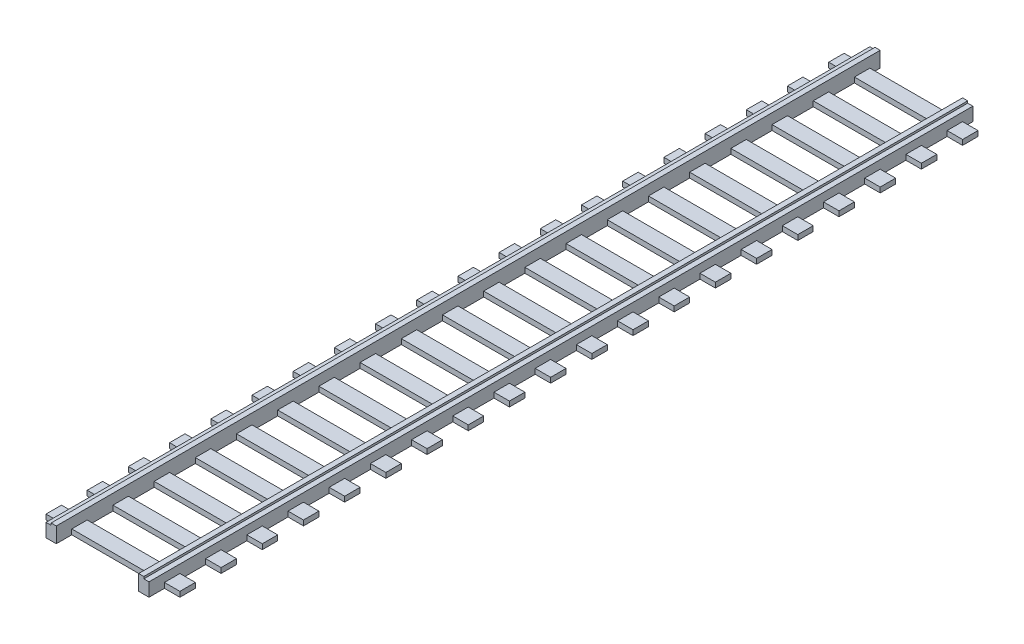
SolidWorks part; units mm, degrees
ref_plane "Front Plane" through (0, 0, 0) normal (0, 0, 1) x (1, 0, 0)
ref_plane "Top Plane" through (0, 0, 0) normal (0, 1, 0) x (1, 0, 0)
ref_plane "Right Plane" through (0, 0, 0) normal (1, 0, 0) x (0, 0, -1)
sketch "Sketch1" plane through (0, 0, 0) normal (0, 1, 0) x (1, 0, 0)
  line L1 (-43.6876, 71.25) -> (-42.6876, 71.25)
  line L2 (-43.6876, 71.25) -> (-43.6876, -88.75)
  line L3 (-43.6876, -88.75) -> (-42.6876, -88.75)
  line L4 (-42.6876, 71.25) -> (-42.6876, -88.75)
  line L5 (-26.6876, 71.25) -> (-25.6876, 71.25)
  line L6 (-26.6876, 71.25) -> (-26.6876, -88.75)
  line L7 (-26.6876, -88.75) -> (-25.6876, -88.75)
  line L8 (-25.6876, 71.25) -> (-25.6876, -88.75)
  dimension "D1" = 160
  dimension "D2" = 1
  dimension "D3" = 1
  dimension "D4" = 16
extrude "Boss-Extrude1" add sketch "Sketch1" along normal blind 3
sketch "Sketch2" plane through (0, 0, 0) normal (0, -1, 0) x (1, 0, 0)
  line L0 (-43.6876, -71.25) -> (-43.6876, 88.75) construction
  line L1 (-43.6876, -71.25) -> (-43.6876, 88.75)
  line L2 (-44.6876, -71.25) -> (-44.6876, 88.75)
  line L3 (-43.6876, -71.25) -> (-44.6876, -71.25)
  line L4 (-43.6876, 88.75) -> (-44.6876, 88.75)
  line L5 (-25.6876, 88.75) -> (-25.6876, -71.25) construction
  line L6 (-25.6876, 88.75) -> (-25.6876, -71.25)
  line L7 (-24.6876, 88.75) -> (-24.6876, -71.25)
  line L8 (-25.6876, 88.75) -> (-24.6876, 88.75)
  line L9 (-25.6876, -71.25) -> (-24.6876, -71.25)
  dimension "D1" = 1
  dimension "D2" = 1
extrude "Boss-Extrude2" add sketch "Sketch2" against normal blind 2.6
sketch "Sketch3" plane through (0, 0, 0) normal (0, -1, 0) x (1, 0, 0)
  line L0 (-44.6876, 88.75) -> (-44.6876, -71.25) construction
  line L1 (-47.6876, 85.75) -> (-21.6876, 85.75)
  line L2 (-47.6876, 85.75) -> (-47.6876, 82.75)
  line L3 (-47.6876, 82.75) -> (-21.6876, 82.75)
  line L4 (-21.6876, 85.75) -> (-21.6876, 82.75)
  line L5 (-24.6876, -71.25) -> (-24.6876, 88.75) construction
  line L6 (-47.6876, 77.75) -> (-47.6876, 74.75)
  line L7 (-47.6876, 77.75) -> (-21.6876, 77.75)
  line L8 (-21.6876, 77.75) -> (-21.6876, 74.75)
  line L9 (-47.6876, 74.75) -> (-21.6876, 74.75)
  line L10 (-47.6876, 69.75) -> (-47.6876, 66.75)
  line L11 (-47.6876, 69.75) -> (-21.6876, 69.75)
  line L12 (-21.6876, 69.75) -> (-21.6876, 66.75)
  line L13 (-47.6876, 66.75) -> (-21.6876, 66.75)
  line L14 (-47.6876, 61.75) -> (-47.6876, 58.75)
  line L15 (-47.6876, 61.75) -> (-21.6876, 61.75)
  line L16 (-21.6876, 61.75) -> (-21.6876, 58.75)
  line L17 (-47.6876, 58.75) -> (-21.6876, 58.75)
  line L18 (-47.6876, 53.75) -> (-47.6876, 50.75)
  line L19 (-47.6876, 53.75) -> (-21.6876, 53.75)
  line L20 (-21.6876, 53.75) -> (-21.6876, 50.75)
  line L21 (-47.6876, 50.75) -> (-21.6876, 50.75)
  line L22 (-47.6876, 45.75) -> (-47.6876, 42.75)
  line L23 (-47.6876, 45.75) -> (-21.6876, 45.75)
  line L24 (-21.6876, 45.75) -> (-21.6876, 42.75)
  line L25 (-47.6876, 42.75) -> (-21.6876, 42.75)
  line L26 (-47.6876, 37.75) -> (-47.6876, 34.75)
  line L27 (-47.6876, 37.75) -> (-21.6876, 37.75)
  line L28 (-21.6876, 37.75) -> (-21.6876, 34.75)
  line L29 (-47.6876, 34.75) -> (-21.6876, 34.75)
  line L30 (-47.6876, 29.75) -> (-47.6876, 26.75)
  line L31 (-47.6876, 29.75) -> (-21.6876, 29.75)
  line L32 (-21.6876, 29.75) -> (-21.6876, 26.75)
  line L33 (-47.6876, 26.75) -> (-21.6876, 26.75)
  line L34 (-47.6876, 21.75) -> (-47.6876, 18.75)
  line L35 (-47.6876, 21.75) -> (-21.6876, 21.75)
  line L36 (-21.6876, 21.75) -> (-21.6876, 18.75)
  line L37 (-47.6876, 18.75) -> (-21.6876, 18.75)
  line L38 (-47.6876, 13.75) -> (-47.6876, 10.75)
  line L39 (-47.6876, 13.75) -> (-21.6876, 13.75)
  line L40 (-21.6876, 13.75) -> (-21.6876, 10.75)
  line L41 (-47.6876, 10.75) -> (-21.6876, 10.75)
  line L42 (-47.6876, 5.75) -> (-47.6876, 2.75)
  line L43 (-47.6876, 5.75) -> (-21.6876, 5.75)
  line L44 (-21.6876, 5.75) -> (-21.6876, 2.75)
  line L45 (-47.6876, 2.75) -> (-21.6876, 2.75)
  line L46 (-47.6876, -2.25) -> (-47.6876, -5.25)
  line L47 (-47.6876, -2.25) -> (-21.6876, -2.25)
  line L48 (-21.6876, -2.25) -> (-21.6876, -5.25)
  line L49 (-47.6876, -5.25) -> (-21.6876, -5.25)
  line L50 (-47.6876, -10.25) -> (-47.6876, -13.25)
  line L51 (-47.6876, -10.25) -> (-21.6876, -10.25)
  line L52 (-21.6876, -10.25) -> (-21.6876, -13.25)
  line L53 (-47.6876, -13.25) -> (-21.6876, -13.25)
  line L54 (-47.6876, -18.25) -> (-47.6876, -21.25)
  line L55 (-47.6876, -18.25) -> (-21.6876, -18.25)
  line L56 (-21.6876, -18.25) -> (-21.6876, -21.25)
  line L57 (-47.6876, -21.25) -> (-21.6876, -21.25)
  line L58 (-47.6876, -26.25) -> (-47.6876, -29.25)
  line L59 (-47.6876, -26.25) -> (-21.6876, -26.25)
  line L60 (-21.6876, -26.25) -> (-21.6876, -29.25)
  line L61 (-47.6876, -29.25) -> (-21.6876, -29.25)
  line L62 (-47.6876, -34.25) -> (-47.6876, -37.25)
  line L63 (-47.6876, -34.25) -> (-21.6876, -34.25)
  line L64 (-21.6876, -34.25) -> (-21.6876, -37.25)
  line L65 (-47.6876, -37.25) -> (-21.6876, -37.25)
  line L66 (-47.6876, -42.25) -> (-47.6876, -45.25)
  line L67 (-47.6876, -42.25) -> (-21.6876, -42.25)
  line L68 (-21.6876, -42.25) -> (-21.6876, -45.25)
  line L69 (-47.6876, -45.25) -> (-21.6876, -45.25)
  line L70 (-47.6876, -50.25) -> (-47.6876, -53.25)
  line L71 (-47.6876, -50.25) -> (-21.6876, -50.25)
  line L72 (-21.6876, -50.25) -> (-21.6876, -53.25)
  line L73 (-47.6876, -53.25) -> (-21.6876, -53.25)
  line L74 (-47.6876, -58.25) -> (-47.6876, -61.25)
  line L75 (-47.6876, -58.25) -> (-21.6876, -58.25)
  line L76 (-21.6876, -58.25) -> (-21.6876, -61.25)
  line L77 (-47.6876, -61.25) -> (-21.6876, -61.25)
  line L78 (-47.6876, -66.25) -> (-47.6876, -69.25)
  line L79 (-47.6876, -66.25) -> (-21.6876, -66.25)
  line L80 (-21.6876, -66.25) -> (-21.6876, -69.25)
  line L81 (-47.6876, -69.25) -> (-21.6876, -69.25)
  dimension "D1" = 3
  dimension "D2" = 3
  dimension "D3" = 3
  dimension "D4" = 3
  dimension "D6" = 3
  dimension "D5" = 20
extrude "Boss-Extrude3" add sketch "Sketch3" against normal blind 1
sketch "Sketch4" plane through (0, 0, -71.25) normal (0, 0, -1) x (-1, 0, 0)
  line L0 (42.6876, 3) -> (43.6876, 3) construction
  line L1 (43.6876, 3) -> (43.6876, 2.6) construction
  line L2 (43.6876, 2.6) -> (44.6876, 2.6) construction
  line L3 (44.6876, 2.6) -> (44.6876, 0) construction
  line L4 (44.6876, 0) -> (42.6876, 0) construction
  line L5 (42.6876, 0) -> (42.6876, 3) construction
  line L6 (26.6876, 3) -> (26.6876, 0) construction
  dimension "D1" = 3
  dimension "D2" = 1
  dimension "D3" = 1
  dimension "D4" = 2.6
  dimension "D5" = 2
  dimension "D6" = 16
